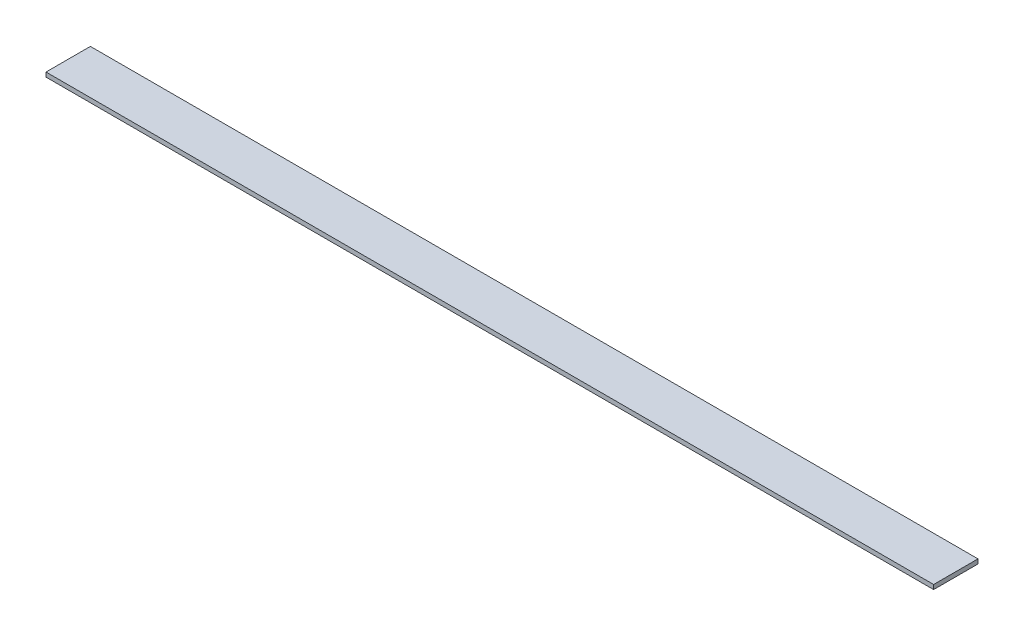
SolidWorks part; units mm, degrees
ref_plane "Front Plane" through (0, 0, 0) normal (0, 0, 1) x (1, 0, 0)
ref_plane "Top Plane" through (0, 0, 0) normal (0, 1, 0) x (1, 0, 0)
ref_plane "Right Plane" through (0, 0, 0) normal (1, 0, 0) x (0, 0, -1)
sketch "Sketch1" plane through (0, 0, 0) normal (0, 1, 0) x (1, 0, 0)
  line L0 (-3000, 150) -> (3000, -150) construction
  line L1 (-3000, 150) -> (3000, 150)
  line L2 (-3000, 150) -> (-3000, -150)
  line L3 (-3000, -150) -> (3000, -150)
  line L4 (3000, 150) -> (3000, -150)
  dimension "D1" = 6000
  dimension "D2" = 300
extrude "Boss-Extrude1" add sketch "Sketch1" along normal blind 30
